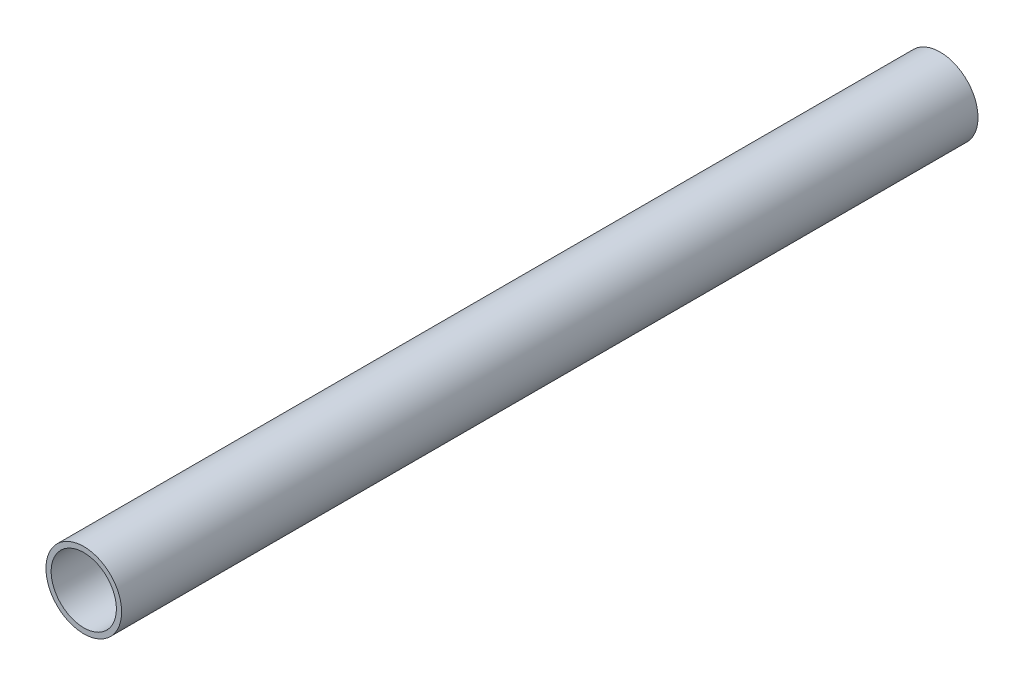
SolidWorks part; units mm, degrees
ref_plane "Front Plane" through (0, 0, 0) normal (0, 0, 1) x (1, 0, 0)
ref_plane "Top Plane" through (0, 0, 0) normal (0, 1, 0) x (1, 0, 0)
ref_plane "Right Plane" through (0, 0, 0) normal (1, 0, 0) x (0, 0, -1)
sketch "Sketch1" plane through (0, 0, 0) normal (0, 0, 1) x (1, 0, 0)
  circle A0 centre (0, 0) radius 3.87
  circle A1 centre (0, 0) radius 4.49
  dimension "D1" = 7.74
  dimension "D2" = 0.62
extrude "Boss-Extrude1" add sketch "Sketch1" along normal blind 101.6
